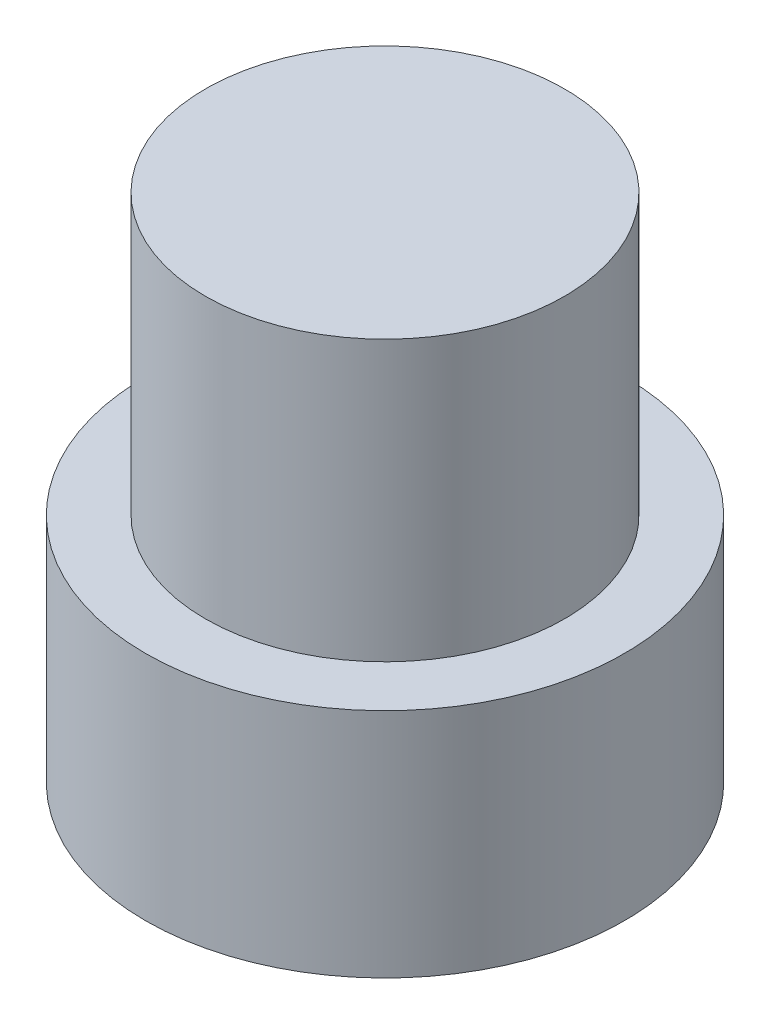
SolidWorks part; units mm, degrees
ref_plane "Front Plane" through (0, 0, 0) normal (0, 0, 1) x (1, 0, 0)
ref_plane "Top Plane" through (0, 0, 0) normal (0, 1, 0) x (1, 0, 0)
ref_plane "Right Plane" through (0, 0, 0) normal (1, 0, 0) x (0, 0, -1)
sketch "Sketch1" plane through (0, 0, 0) normal (0, 1, 0) x (1, 0, 0)
  circle A0 centre (0, 0) radius 6
extrude "Boss-Extrude2" add sketch "Sketch1" against normal blind 5.8
sketch "Sketch5" plane through (0, 0, 0) normal (0, 1, 0) x (-1, 0, 0)
  circle A0 centre (0, 0) radius 4.5
extrude "Boss-Extrude3" add sketch "Sketch5" along normal blind 7
sketch "Sketch6" plane through (0, -5.8, 0) normal (0, -1, 0) x (1, 0, 0)
  circle A0 centre (0, 0) radius 2.5
extrude "Boss-Extrude4" add sketch "Sketch6" along normal blind 1.5
